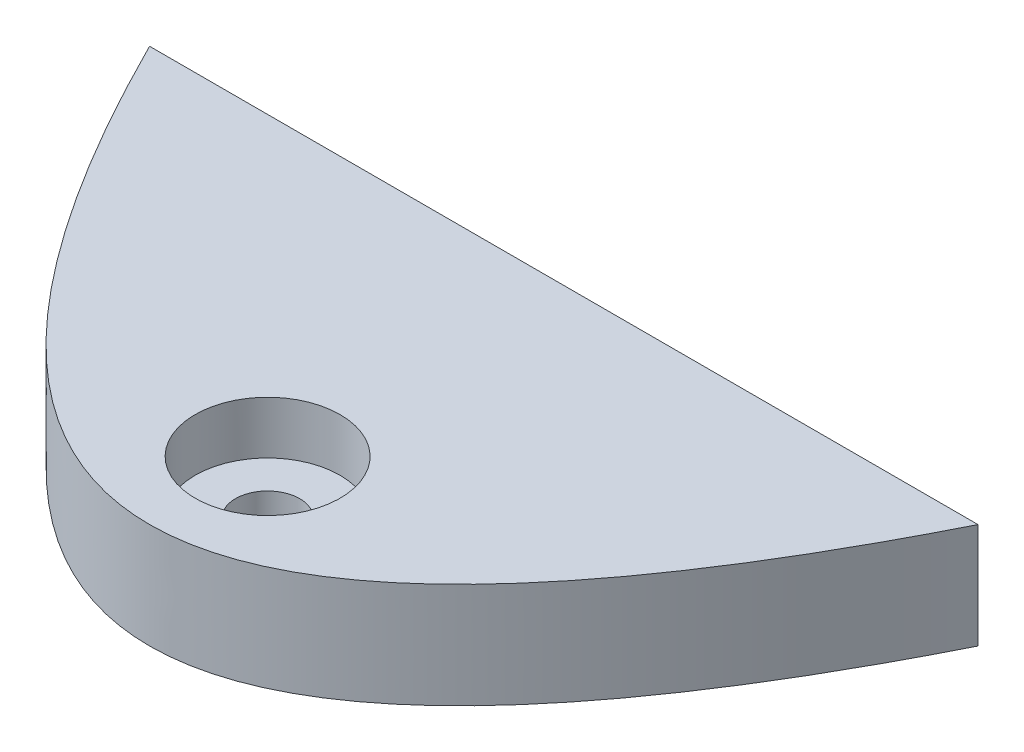
SolidWorks part; units mm, degrees
material "Custom Plastic (2)"
ref_plane "Front Plane" through (0, 0, 0) normal (0, 0, 1) x (1, 0, 0)
ref_plane "Top Plane" through (0, 0, 0) normal (0, 1, 0) x (1, 0, 0)
ref_plane "Right Plane" through (0, 0, 0) normal (1, 0, 0) x (0, 0, -1)
sketch "Sketch1" plane through (0, 0, 0) normal (0, 1, 0) x (1, 0, 0)
  line L0 (-200, 0) -> (200, 0)
  spline S0 degree 2 poles (-225.2396, 53.6645) (0, -453.6645) (225.2396, 53.6645) knots 0 0 0 1 1 1 construction
  spline S1 degree 2 poles (-200, 0) (0, -400) (200, 0) knots 0.056028 0.056028 0.056028 0.943972 0.943972 0.943972
extrude "Boss-Extrude1" add sketch "Sketch1" along normal blind 300
sketch "Sketch2" plane through (0, 300, 0) normal (0, 1, 0) x (1, 0, 0)
  line L0 (0, 200) -> (0, -200)
  line L2 (200, 0) -> (-200, 0) construction
  circle A0 centre (0, -143) radius 35
  parabola Q0 (-200, 0) -> (200, 0) focus (0, -150) apex (0, -200) construction
  point P4 (0, 0)
  dimension "D1" = 70
  dimension "D2" = 143
ref_plane "Plane1" through (0, 150, 0) normal (0, 1, 0) x (1, 0, 0)
sketch "Sketch3" plane through (0, 150, 0) normal (0, 1, 0) x (1, 0, 0)
  circle A0 centre (0, -143) radius 15.5
  dimension "D1" = 31
extrude "Cut-Extrude1" cut sketch "Sketch3" against normal blind 23 and the other way blind 23
ref_plane "Plane2" through (0, 173, 0) normal (0, 1, 0) x (1, 0, 0)
sketch "Sketch4" plane through (0, 173, 0) normal (0, 1, 0) x (1, 0, 0)
  circle A0 centre (0, -143) radius 35
extrude "Cut-Extrude3" cut sketch "Sketch4" along normal blind 300 contours A0
mirror "Mirror1" about plane through (0, 150, 0) normal (0, 1, 0) of "Cut-Extrude3"
sketch "Sketch5" plane through (0, 0, 0) normal (0, 0, -1) x (-1, 0, 0)
  line L0 (-200, 300) -> (200, 300) construction
  line L1 (-249.3315, 147.6) -> (292.2272, 147.6)
  line L2 (-249.3315, 147.6) -> (-249.3315, -63.4665)
  line L3 (-249.3315, -63.4665) -> (292.2272, -63.4665)
  line L4 (292.2272, 147.6) -> (292.2272, -63.4665)
  line L6 (-262.0052, 304.6644) -> (267.3672, 304.6644)
  line L7 (-262.0052, 304.6644) -> (-262.0052, 198.4)
  line L8 (-262.0052, 198.4) -> (267.3672, 198.4)
  line L9 (267.3672, 304.6644) -> (267.3672, 198.4)
  dimension "D1" = 152.4
  dimension "D2" = 101.6
extrude "Cut-Extrude4" cut sketch "Sketch5" against normal through all
